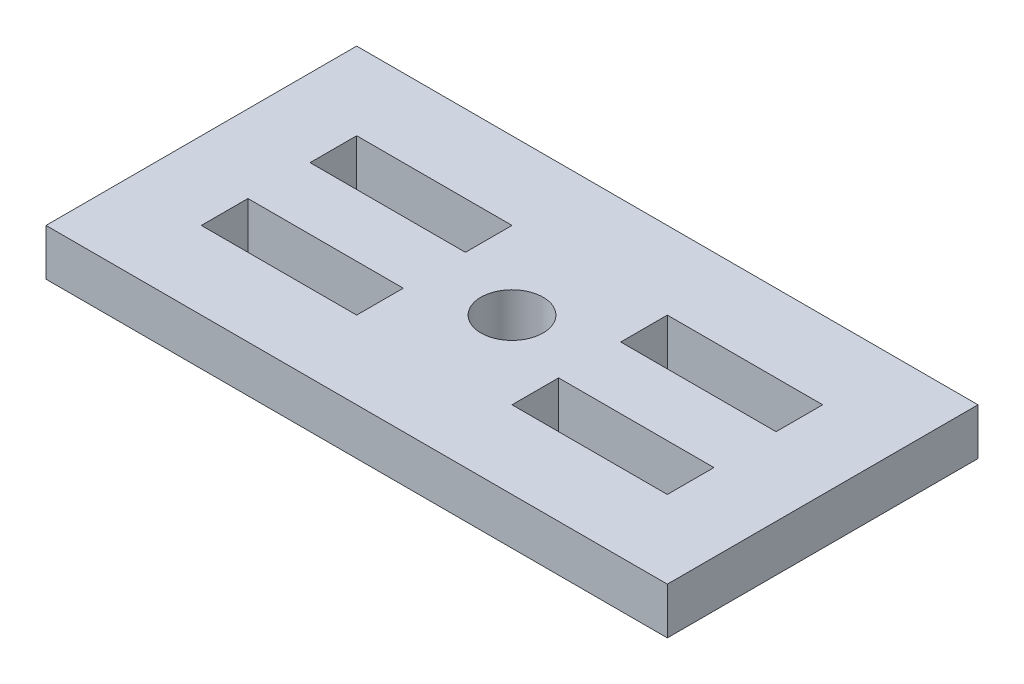
SolidWorks part; units mm, degrees
ref_plane "Front Plane" through (0, 0, 0) normal (0, 0, 1) x (1, 0, 0)
ref_plane "Top Plane" through (0, 0, 0) normal (0, 1, 0) x (1, 0, 0)
ref_plane "Right Plane" through (0, 0, 0) normal (1, 0, 0) x (0, 0, -1)
sketch "Sketch1" plane through (0, 0, 0) normal (0, 1, 0) x (1, 0, 0)
  line L1 (-7.7249, 4.6296) -> (12.2751, 4.6296)
  line L2 (-7.7249, 4.6296) -> (-7.7249, -5.3704)
  line L3 (-7.7249, -5.3704) -> (12.2751, -5.3704)
  line L4 (12.2751, 4.6296) -> (12.2751, -5.3704)
  dimension "D1" = 10
  dimension "D2" = 20
extrude "Boss-Extrude1" add sketch "Sketch1" along normal blind 1.5
sketch "Sketch2" plane through (0, 1.5, 0) normal (0, 1, 0) x (1, 0, 0)
  line L4 (12.2751, 4.6296) -> (-7.7249, 4.6296) construction
  line L5 (2.2751, 4.6296) -> (2.2751, -5.3704) construction
  line L6 (-7.7249, -0.3704) -> (12.2751, -0.3704) construction
  line L7 (-7.7249, 4.6296) -> (-7.7249, -5.3704) construction
  line L8 (12.2751, -5.3704) -> (12.2751, 4.6296) construction
  circle A0 centre (2.2751, -0.3704) radius 1
  dimension "D1" = 2
sketch "Sketch3" plane through (0, 1.5, 0) normal (0, 1, 0) x (1, 0, 0)
  line L0 (2.2751, 4.6296) -> (2.2751, -5.3704) construction
  line L1 (-5.2249, 2.1296) -> (-0.2249, 2.1296)
  line L2 (-5.2249, 2.1296) -> (-5.2249, 0.6296)
  line L3 (-5.2249, 0.6296) -> (-0.2249, 0.6296)
  line L4 (-0.2249, 2.1296) -> (-0.2249, 0.6296)
  line L5 (4.7751, 0.6296) -> (9.7751, 0.6296)
  line L6 (4.7751, 0.6296) -> (4.7751, 2.1296)
  line L7 (4.7751, 2.1296) -> (9.7751, 2.1296)
  line L8 (9.7751, 0.6296) -> (9.7751, 2.1296)
  line L9 (9.7751, -2.8704) -> (4.7751, -2.8704)
  line L10 (9.7751, -2.8704) -> (9.7751, -1.3704)
  line L11 (9.7751, -1.3704) -> (4.7751, -1.3704)
  line L12 (4.7751, -2.8704) -> (4.7751, -1.3704)
  line L13 (-0.2249, -2.8704) -> (-5.2249, -2.8704)
  line L14 (-0.2249, -2.8704) -> (-0.2249, -1.3704)
  line L15 (-0.2249, -1.3704) -> (-5.2249, -1.3704)
  line L16 (-5.2249, -2.8704) -> (-5.2249, -1.3704)
  line L17 (-7.7249, -0.3704) -> (12.2751, -0.3704) construction
  point P16 (-0.2249, 1.3796)
  dimension "D1" = 5
  dimension "D2" = 2.5
  dimension "D3" = 2
  dimension "D4" = 1
  dimension "D5" = 1.5
  dimension "D6" = 5
extrude "Cut-Extrude1" cut sketch "Sketch3" against normal blind 2
extrude "Cut-Extrude2" cut sketch "Sketch2" against normal blind 2 contours A0
